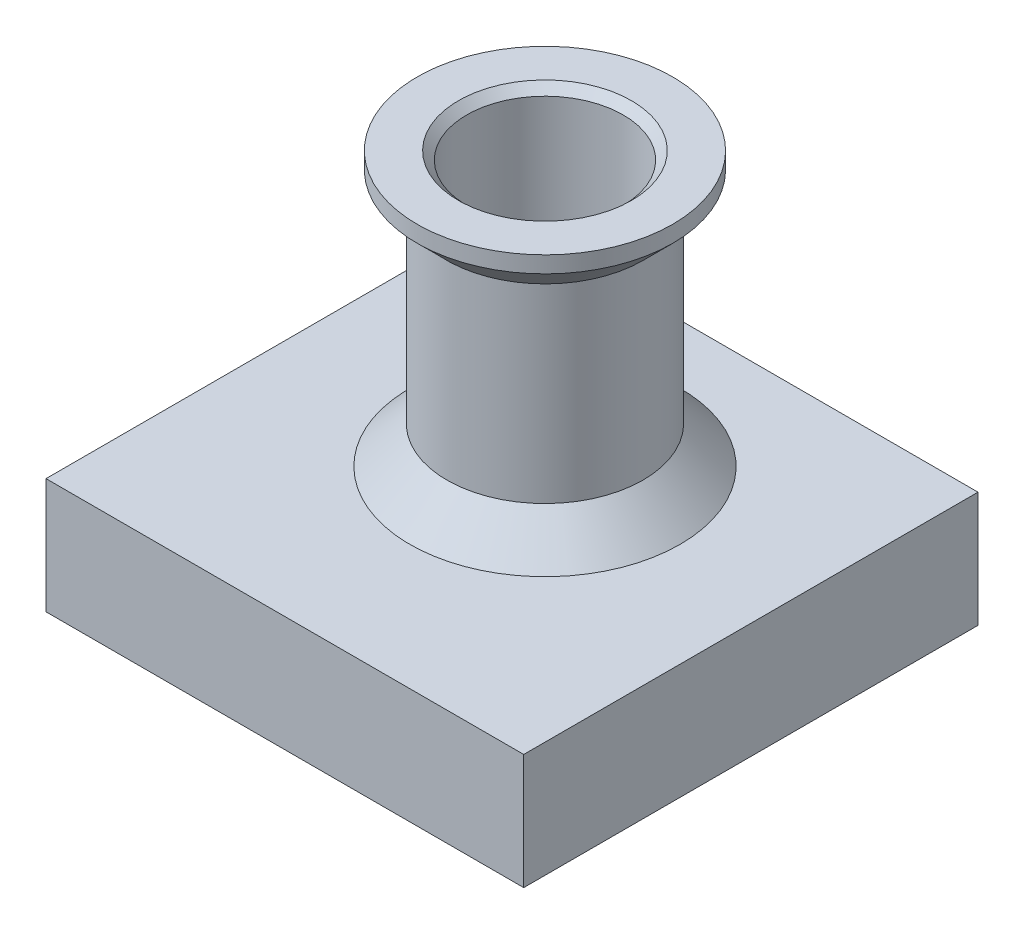
SolidWorks part; units mm, degrees
ref_plane "Front Plane" through (0, 0, 0) normal (0, 0, 1) x (1, 0, 0)
ref_plane "Top Plane" through (0, 0, 0) normal (0, 1, 0) x (1, 0, 0)
ref_plane "Right Plane" through (0, 0, 0) normal (1, 0, 0) x (0, 0, -1)
sketch "Sketch1" plane through (0, 0, 0) normal (0, 0, 1) x (1, 0, 0)
  line L0 (0, -12.9233) -> (0, 12.9233) construction
  line L1 (-19.3603, 0) -> (19.3603, 0) construction
  line L2 (4.75, 9.5) -> (4.75, 0)
  line L3 (5.25, 10) -> (7.75, 10)
  line L4 (7.75, 10) -> (7.75, 9)
  line L5 (7.75, 9) -> (5.95, 7.2)
  line L8 (5.95, 7.2) -> (5.95, -4.3426)
  line L9 (4.75, 9.5) -> (5.25, 10)
  line L13 (3.6, -13.5935) -> (3.6, -1.15)
  line L14 (3.6, -1.15) -> (4.75, 0)
  line L15 (8.2008, -6.5935) -> (22, -6.5935)
  line L16 (22, -6.5935) -> (22, -13.5935)
  line L18 (22, -13.5935) -> (3.6, -13.5935)
  line L19 (8.2008, -6.5935) -> (5.95, -4.3426)
  point P0 (4.75, 10)
  point P4 (0, 0)
  point P7 (0, 0)
  point P9 (5.95, 0)
  dimension "D1" = 4.75
  dimension "D2" = 3
  dimension "D3" = 10
  dimension "D4" = 1
  dimension "D5" = 5.95
  dimension "D6" = 45
  dimension "D7" = 45
  dimension "D8" = 45
  dimension "D9" = 7
  dimension "D10" = 3.6
  dimension "D12" = 22
revolve "Revolve1" add sketch "Sketch1" angle 360 about L0
sketch "Sketch2" plane through (0, 0, 0) normal (0, 1, 0) x (1, 0, 0)
  line L1 (-14.4934, 11.7819) -> (14.4934, 11.7819)
  line L2 (-14.4934, 11.7819) -> (-14.4934, -15.7819)
  line L3 (-14.4934, -15.7819) -> (14.4934, -15.7819)
  line L4 (14.4934, 11.7819) -> (14.4934, -15.7819)
  line L5 (-14.4934, 11.7819) -> (14.4934, -15.7819) construction
  line L6 (-14.4934, -15.7819) -> (14.4934, 11.7819) construction
  point P0 (0, -2)
extrude "Cut-Extrude1" cut sketch "Sketch2" against normal through all both and the other way through all flip side to cut
ref_plane "Plane1" through (0, -14.5935, 0) normal (0, -1, 0) x (-1, 0, 0)
sketch "Sketch3" plane through (0, -14.5935, 0) normal (0, -1, 0) x (-1, 0, 0)
  line L0 (0, -15.8502) -> (0, 15.8502) construction
  line L1 (-16.5897, 0) -> (16.5897, 0) construction
  line L2 (-8.5, 4.285) -> (8.5, 4.285)
  line L3 (-8.5, -12.715) -> (8.5, -12.715)
  line L4 (-8.5, 4.285) -> (-8.5, -12.715)
  line L5 (8.5, 4.285) -> (8.5, -12.715)
  point P4 (0, 0)
  point P8 (0, 0)
  point P9 (0, 0)
  point P12 (19.1481, -12.715)
  dimension "D1" = 4.285
  dimension "D2" = 17
  dimension "D3" = 8.5
  dimension "D4" = 8.5
extrude "Cut-Extrude2" cut sketch "Sketch3" against normal blind 6.5
equation "\"D4@Sketch3\"=\"D3@Sketch3\""
